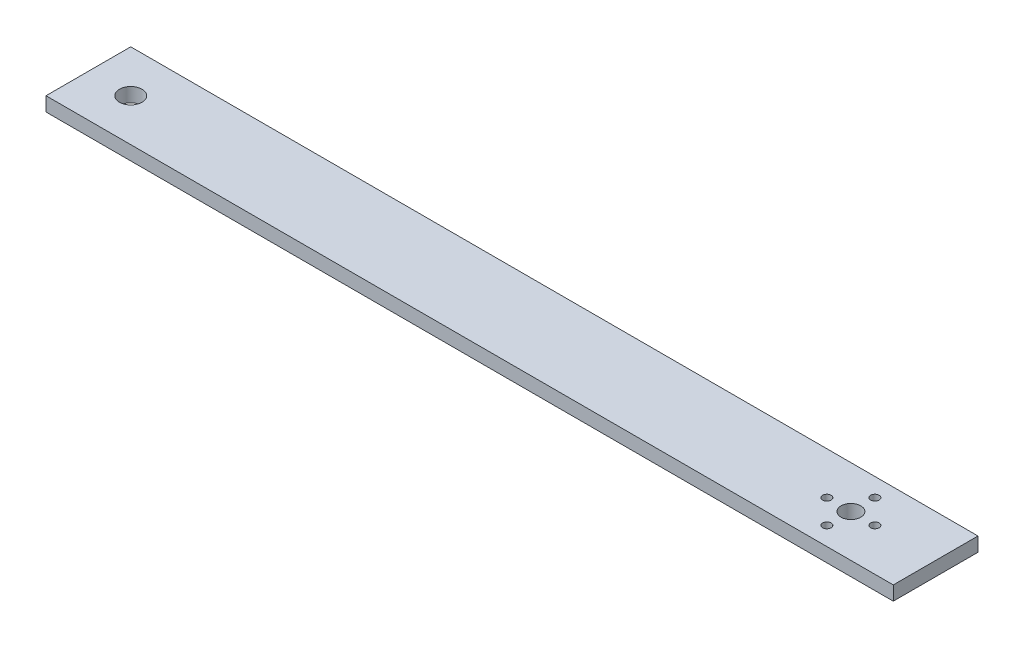
SolidWorks part; units mm, degrees
ref_plane "Front Plane" through (0, 0, 0) normal (0, 0, 1) x (1, 0, 0)
ref_plane "Top Plane" through (0, 0, 0) normal (0, 1, 0) x (1, 0, 0)
ref_plane "Right Plane" through (0, 0, 0) normal (1, 0, 0) x (0, 0, -1)
sketch "Sketch1" plane through (0, 0, 0) normal (0, 1, 0) x (1, 0, 0)
  line L1 (0, 0) -> (300, 0)
  line L2 (0, 0) -> (0, 30)
  line L3 (0, 30) -> (300, 30)
  line L4 (300, 0) -> (300, 30)
  circle A0 centre (15, 15) radius 4
  circle A1 centre (270, 15) radius 3.5
  circle A3 centre (278.5, 15) radius 1.5
  circle A4 centre (261.5, 15) radius 1.5
  circle A5 centre (270, 23.5) radius 1.5
  circle A6 centre (270, 6.5) radius 1.5
  dimension "D1" = 30
  dimension "D2" = 300
extrude "Boss-Extrude1" add sketch "Sketch1" along normal blind 5
sketch "Sketch2" plane through (0, 5, 0) normal (0, 1, 0) x (1, 0, 0)
  circle A0 centre (15, 15) radius 4
  circle A1 centre (185, 15) radius 3.5
  circle A3 centre (185, 23.5) radius 1.5
  circle A4 centre (193.4791, 15) radius 1.5
  circle A5 centre (176.5209, 15) radius 1.5
  circle A6 centre (185, 6.5) radius 1.5
